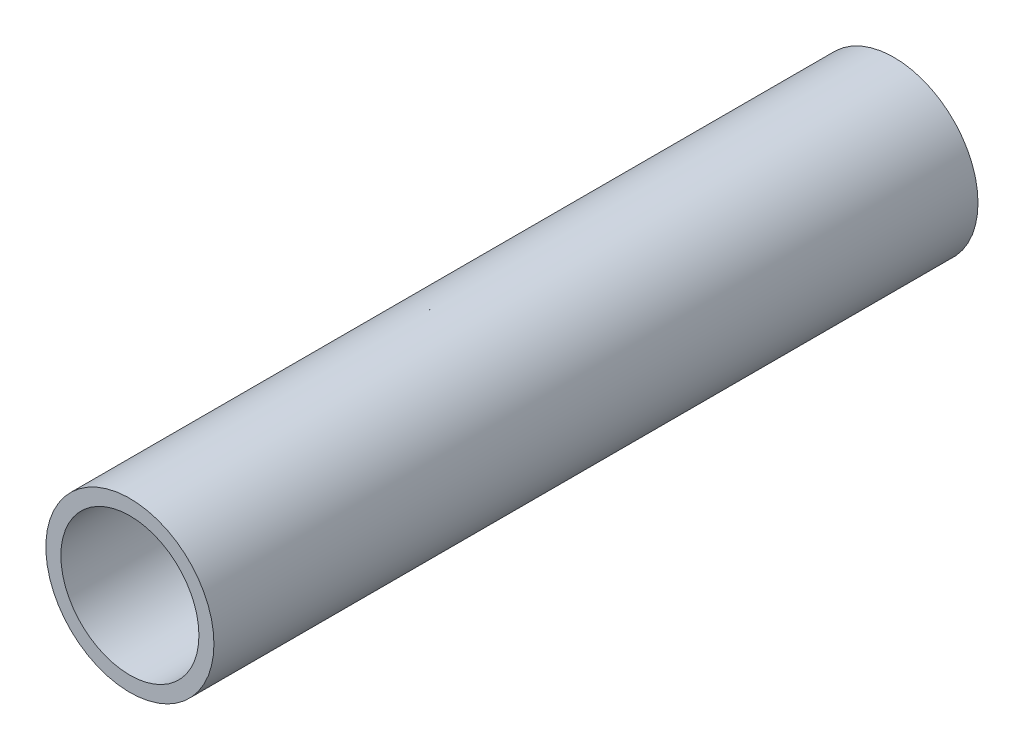
SolidWorks part; units mm, degrees
ref_plane "Front Plane" through (0, 0, 0) normal (0, 0, 1) x (1, 0, 0)
ref_plane "Top Plane" through (0, 0, 0) normal (0, 1, 0) x (1, 0, 0)
ref_plane "Right Plane" through (0, 0, 0) normal (1, 0, 0) x (0, 0, -1)
sketch "Sketch1" plane through (0, 0, 0) normal (0, 0, 1) x (1, 0, 0)
  circle A0 centre (0, 0) radius 2.794
  circle A1 centre (0, 0) radius 2.295
  dimension "D1" = 5.588
  dimension "D2" = 4.59
extrude "Boss-Extrude1" add sketch "Sketch1" along normal blind 25.4
ref_plane "Plane1" through (0, 0, 0) normal (0, 0, -1) x (-1, 0, 0)
ref_plane "Plane2" through (0, 0, 9.652) normal (0, 0, -1) x (-1, 0, 0)
sketch "Sketch4" plane through (0, 0, 9.652) normal (0, 0, -1) x (-1, 0, 0)
  circle A0 centre (0, 0) radius 2.295 construction
  circle A1 centre (0, 0) radius 2.295
  circle A2 centre (0, 0) radius 1.778
  dimension "D1" = 3.556
extrude "Boss-Extrude2" add sketch "Sketch4" along normal blind 0.635
